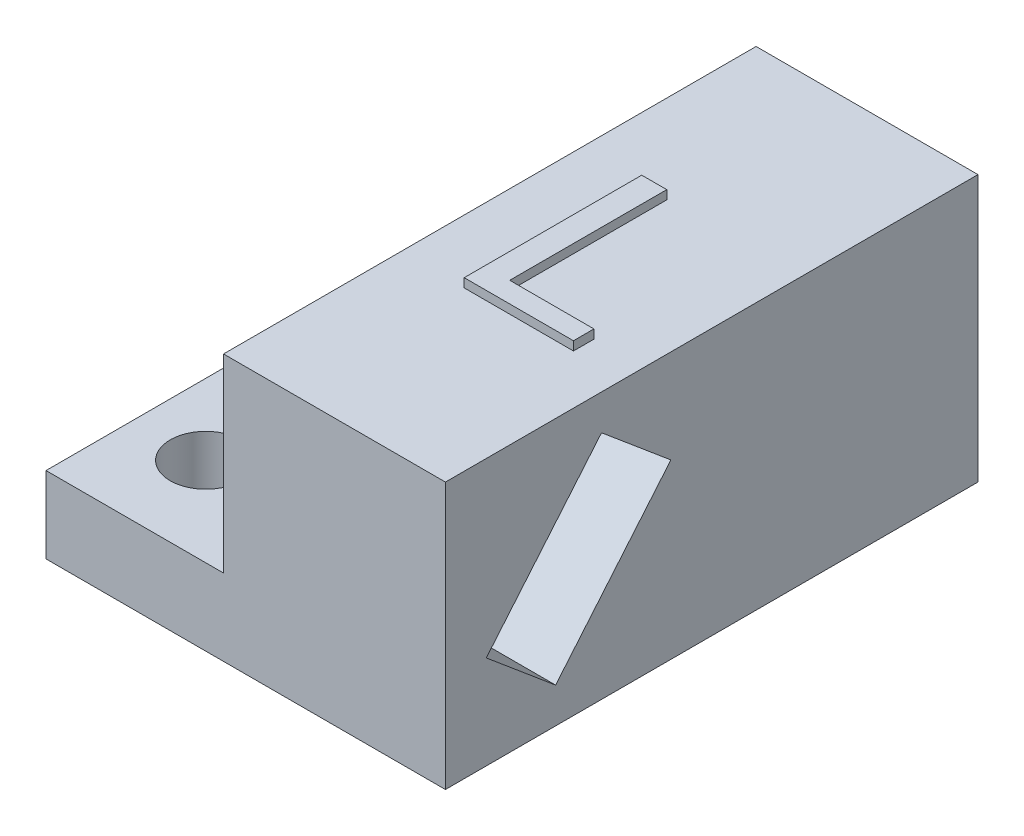
SolidWorks part; units mm, degrees
ref_plane "Спереди" through (0, 0, 0) normal (0, 0, 1) x (1, 0, 0)
ref_plane "Сверху" through (0, 0, 0) normal (0, 1, 0) x (1, 0, 0)
ref_plane "Справа" through (0, 0, 0) normal (1, 0, 0) x (0, 0, -1)
sketch "Sketch1" plane through (0, 0, 0) normal (0, 1, 0) x (1, 0, 0)
  line L1 (12.5, -30) -> (-12.5, -30)
  line L2 (12.5, -30) -> (12.5, 30)
  line L3 (12.5, 30) -> (-12.5, 30)
  line L4 (-12.5, -30) -> (-12.5, 30)
  line L5 (12.5, -30) -> (-12.5, 30) construction
  line L6 (12.5, 30) -> (-12.5, -30) construction
  point P0 (0, 0)
  dimension "D1" = 25
  dimension "D2" = 60
extrude "Boss-Extrude1" add sketch "Sketch1" along normal blind 30
sketch "Sketch2" plane through (-12.5, 0, 0) normal (-1, 0, 0) x (0, 0, 1)
  line L0 (-30, 4.3119) -> (30, 4.3119) construction
  line L1 (-30, 30) -> (-30, 0) construction
  line L2 (30, 30) -> (30, 0) construction
  line L4 (30, 8.6238) -> (-30, 8.6238)
  line L5 (30, 8.6238) -> (30, 0)
  line L6 (30, 0) -> (-30, 0)
  line L7 (-30, 8.6238) -> (-30, 0)
  line L8 (30, 8.6238) -> (-30, 0) construction
  line L9 (30, 0) -> (-30, 8.6238) construction
  point P6 (0, 4.3119)
extrude "Boss-Extrude2" add sketch "Sketch2" along normal blind 20
sketch "Sketch3" plane through (0, 8.6238, 0) normal (0, 1, 0) x (1, 0, 0)
  line L0 (-24.5, -30) -> (-24.5, 30) construction
  line L1 (-32.5, 30) -> (-12.5, 30) construction
  line L2 (-32.5, -30) -> (-12.5, -30) construction
  circle A0 centre (-24.5, 20) radius 4
  circle A1 centre (-24.5, -20) radius 4
  dimension "D1" = 8
  dimension "D2" = 8
  dimension "D3" = 10
  dimension "D4" = 10
extrude "Cut-Extrude1" cut sketch "Sketch3" against normal through all
sketch "Sketch4" plane through (12.5, 0, 0) normal (1, 0, 0) x (0, 0, -1)
  line L0 (-15, 30) -> (-15, 0) construction
  line L1 (-17.5853, 3.9847) -> (-4.601, 19.4588)
  line L2 (-17.5853, 3.9847) -> (-25.399, 10.5412)
  line L3 (-30, 30) -> (30, 30) construction
  line L4 (-9.9, 4.9) -> (-20.1, 4.9) construction
  line L5 (-9.9, 4.9) -> (-9.9, 25.1) construction
  line L6 (-9.9, 25.1) -> (-20.1, 25.1) construction
  line L7 (-20.1, 4.9) -> (-20.1, 25.1) construction
  line L8 (-9.9, 4.9) -> (-20.1, 25.1) construction
  line L9 (-9.9, 25.1) -> (-20.1, 4.9) construction
  line L10 (-30, 0) -> (30, 0) construction
  line L11 (-4.601, 19.4588) -> (-12.4147, 26.0153)
  line L12 (-25.399, 10.5412) -> (-12.4147, 26.0153)
  line L13 (-8.5078, 22.737) -> (-21.4922, 7.263) construction
  line L14 (-11.0932, 11.7218) -> (-18.9068, 18.2782) construction
  line L15 (-30, 30) -> (-30, 0) construction
  point P6 (-15, 15)
  point P12 (-15, 15)
  point P13 (-15, 15)
  dimension "D1" = 20.2
  dimension "D2" = 10.2
  dimension "D3" = 15
  dimension "D4" = 10.2
  dimension "D5" = 20.2
  dimension "D6" = 40
extrude "Cut-Extrude2" cut sketch "Sketch4" against normal blind 20
sketch "Sketch5" plane through (0, 30, 0) normal (0, 1, 0) x (1, 0, 0)
  line L0 (12.5, -10) -> (-12.5, -10) construction
  line L1 (12.5, -30) -> (12.5, 30) construction
  line L2 (-12.5, 30) -> (-12.5, -30) construction
  text T0 "L" font "Arial" height 20
  dimension "D1" = 20
extrude "Boss-Extrude3" add sketch "Sketch5" along normal blind 1
